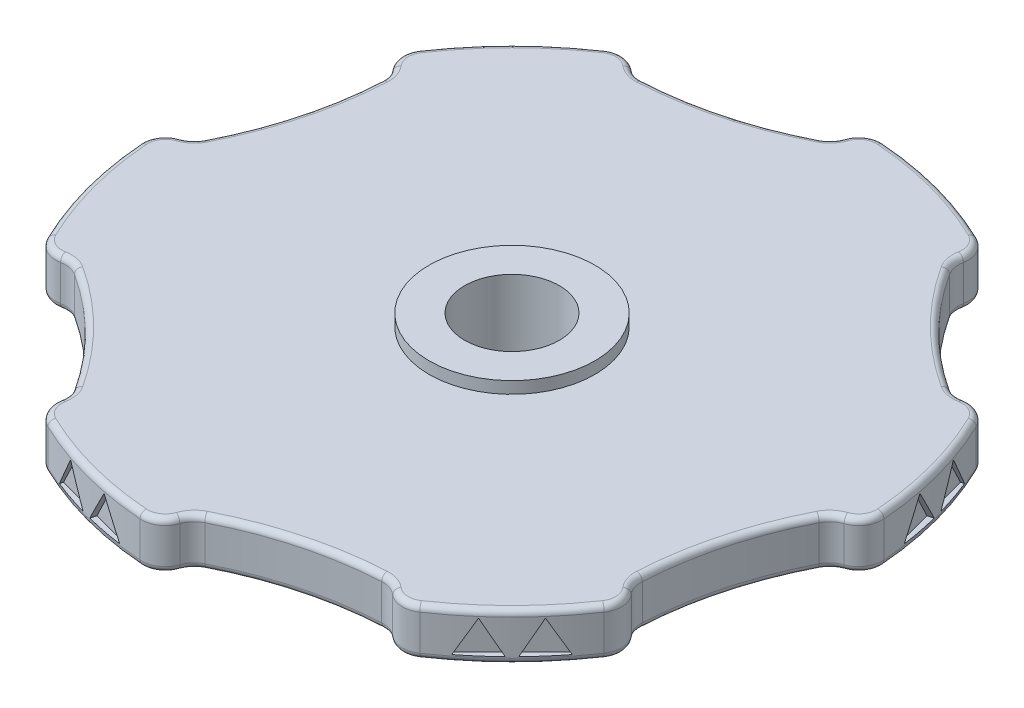
SolidWorks part; units mm, degrees
material "ABS"
ref_plane "前视基准面" through (0, 0, 0) normal (0, 0, 1) x (1, 0, 0)
ref_plane "上视基准面" through (0, 0, 0) normal (0, 1, 0) x (1, 0, 0)
ref_plane "右视基准面" through (0, 0, 0) normal (1, 0, 0) x (0, 0, -1)
other "Configuration Table"
sketch "草图1" plane through (0, 0, 0) normal (0, 1, 0) x (1, 0, 0)
  line L0 (0, 0) -> (0, -27.2667)
  line L1 (29.34, 0) -> (25.4092, 14.67) construction
  line L2 (25.4092, 14.67) -> (14.67, 25.4092) construction
  line L3 (14.67, 25.4092) -> (0, 29.34) construction
  line L4 (0, 29.34) -> (-14.67, 25.4092) construction
  line L5 (-14.67, 25.4092) -> (-25.4092, 14.67) construction
  line L6 (-25.4092, 14.67) -> (-29.34, 0) construction
  line L7 (-29.34, 0) -> (-25.4092, -14.67) construction
  line L8 (-25.4092, -14.67) -> (-14.67, -25.4092) construction
  line L9 (-14.67, -25.4092) -> (0, -29.34) construction
  line L10 (0, -29.34) -> (14.67, -25.4092) construction
  line L11 (14.67, -25.4092) -> (25.4092, -14.67) construction
  line L12 (25.4092, -14.67) -> (29.34, 0) construction
  line L13 (0, 0) -> (-13.6334, -23.6137)
  line L14 (13.6334, -23.6137) -> (0, 0)
  line L15 (0, 0) -> (-23.6137, -13.6334)
  line L16 (0, 0) -> (-27.2667, 0)
  line L17 (-13.6334, -23.6137) -> (0, 0)
  line L18 (0, 0) -> (-23.6137, 13.6334)
  line L19 (0, 0) -> (-13.6334, 23.6137)
  line L20 (-27.2667, 0) -> (0, 0)
  line L21 (0, 0) -> (0, 27.2667)
  line L22 (0, 0) -> (13.6334, 23.6137)
  line L23 (-13.6334, 23.6137) -> (0, 0)
  line L24 (0, 0) -> (23.6137, 13.6334)
  line L25 (0, 0) -> (27.2667, 0)
  line L26 (13.6334, 23.6137) -> (0, 0)
  line L27 (0, 0) -> (23.6137, -13.6334)
  line L28 (0, 0) -> (13.6334, -23.6137)
  line L29 (27.2667, 0) -> (0, 0)
  circle A1 centre (0, 0) radius 29.34 construction
  arc A2 (-12.7719, -26.4143) -> (-2.1463, -29.2614) centre (0, 0) ccw
  arc A3 (0, -27.2667) -> (-2.1463, -29.2614) centre (-2, -27.2667) cw
  arc A4 (-13.6334, -23.6137) -> (-12.7719, -26.4143) centre (-11.9013, -24.6137) ccw
  arc A5 (0, -29.34) -> (12.7719, -26.4143) centre (0, 0) ccw
  arc A6 (12.7719, -26.4143) -> (13.6334, -23.6137) centre (11.9013, -24.6137) ccw
  arc A7 (0, -27.2667) -> (13.6334, -23.6137) centre (14.1875, -52.9485) cw
  arc A8 (-29.2614, -2.1463) -> (-26.4143, -12.7719) centre (0, 0) ccw
  arc A9 (-27.2667, 0) -> (-29.2614, -2.1463) centre (-27.2667, -2) ccw
  arc A10 (-23.6137, -13.6334) -> (-26.4143, -12.7719) centre (-24.6137, -11.9013) cw
  arc A11 (-23.6137, -13.6334) -> (-13.6334, -23.6137) centre (-38.761, -38.761) cw
  arc A12 (-16.4895, 24.268) -> (-24.268, 16.4895) centre (0, 0) ccw
  arc A13 (-13.6334, 23.6137) -> (-16.4895, 24.268) centre (-15.3654, 22.6137) ccw
  arc A14 (-23.6137, 13.6334) -> (-24.268, 16.4895) centre (-22.6137, 15.3654) cw
  arc A15 (-23.6137, 13.6334) -> (-27.2667, 0) centre (-52.9485, 14.1875) cw
  arc A16 (12.7719, 26.4143) -> (2.1463, 29.2614) centre (0, 0) ccw
  arc A17 (13.6334, 23.6137) -> (12.7719, 26.4143) centre (11.9013, 24.6137) ccw
  arc A18 (0, 27.2667) -> (2.1463, 29.2614) centre (2, 27.2667) cw
  arc A19 (0, 27.2667) -> (-13.6334, 23.6137) centre (-14.1875, 52.9485) cw
  arc A20 (29.2614, 2.1463) -> (26.4143, 12.7719) centre (0, 0) ccw
  arc A21 (27.2667, 0) -> (29.2614, 2.1463) centre (27.2667, 2) ccw
  arc A22 (23.6137, 13.6334) -> (26.4143, 12.7719) centre (24.6137, 11.9013) cw
  arc A23 (23.6137, 13.6334) -> (13.6334, 23.6137) centre (38.761, 38.761) cw
  arc A24 (16.4895, -24.268) -> (24.268, -16.4895) centre (0, 0) ccw
  arc A25 (13.6334, -23.6137) -> (16.4895, -24.268) centre (15.3654, -22.6137) ccw
  arc A26 (23.6137, -13.6334) -> (24.268, -16.4895) centre (22.6137, -15.3654) cw
  arc A27 (23.6137, -13.6334) -> (27.2667, 0) centre (52.9485, -14.1875) cw
  point P70 (0, 0)
  dimension "D1" = 58.68
  dimension "D2" = 2
  dimension "D3" = 2
  dimension "D4" = 6
extrude "凸台-拉伸2" add sketch "草图1" along normal blind 4 contours A10 L15 L16 A9 A8 | L15 A11 L13 | L13 A4 A2 A3 L0 | L0 A7 L14 | A26 L27 L14 A25 A24 | L27 A27 L25 | A22 L24 L25 A21 A20 | L24 A23 L22 | A18 L21 L22 A17 A16 | L21 A19 L19 | A14 L18 L19 A13 A12 | L18 A15 L16
fillet "圆角2" radius 2 12 edges at (13.6334, 2, 23.6137) (0, 2, 27.2667) (-13.6334, 2, 23.6137) (-23.6137, 2, 13.6334) (-27.2667, 2, 0) (-23.6137, 2, -13.6334) (-13.6334, 2, -23.6137) (0, 2, -27.2667) (13.6334, 2, -23.6137) (23.6137, 2, -13.6334) (27.2667, 2, 0) (23.6137, 2, 13.6334)
fillet "圆角1" radius 0.5 72 edges at (24.6105, 4, 15.2518) (20.7465, 4, 20.7465) (15.2518, 4, 24.6105) (6.5937, 4, 24.6082) (-0.9032, 4, 28.9392) (-7.5938, 4, 28.3403) (-13.6874, 4, 25.5137) (-18.0145, 4, 18.0145) (-25.5137, 4, 13.6874) (-28.3403, 4, 7.5938) (-28.9392, 4, 0.9032) (-24.6082, 4, -6.5937) (-24.6105, 4, -15.2518) (-20.7465, 4, -20.7465) (-15.2518, 4, -24.6105) (-6.5937, 4, -24.6082) (0.9032, 4, -28.9392) (7.5938, 4, -28.3403) (13.6874, 4, -25.5137) (18.0145, 4, -18.0145) (25.5137, 4, -13.6874) (28.3403, 4, -7.5938) (28.9392, 4, -0.9032) (24.6082, 4, 6.5937) (28.9392, 0, -0.9032) (28.3403, 0, -7.5938) (25.5137, 0, -13.6874) (18.0145, 0, -18.0145) (13.6874, 0, -25.5137) (7.5938, 0, -28.3403) (0.9032, 0, -28.9392) (-6.5937, 0, -24.6082) (-15.2518, 0, -24.6105) (-20.7465, 0, -20.7465) (-24.6105, 0, -15.2518) (-24.6082, 0, -6.5937) (-28.9392, 0, 0.9032) (-28.3403, 0, 7.5938) (-25.5137, 0, 13.6874) (-18.0145, 0, 18.0145) (-13.6874, 0, 25.5137) (-7.5938, 0, 28.3403) (-0.9032, 0, 28.9392) (6.5937, 0, 24.6082) (15.2518, 0, 24.6105) (20.7465, 0, 20.7465) (24.6105, 0, 15.2518) (24.6082, 0, 6.5937) (13.403, 4, 23.7532) (0.2693, 4, 27.2724) (-13.8694, 4, 23.4839) (-23.4839, 4, 13.8694) (-27.2724, 4, -0.2693) (-23.7532, 4, -13.403) (-13.403, 4, -23.7532) (-0.2693, 4, -27.2724) (13.8694, 4, -23.4839) (23.4839, 4, -13.8694) (27.2724, 4, 0.2693) (23.7532, 4, 13.403) (27.2724, 0, 0.2693) (23.4839, 0, -13.8694) (13.8694, 0, -23.4839) (-0.2693, 0, -27.2724) (-13.403, 0, -23.7532) (-23.7532, 0, -13.403) (-27.2724, 0, -0.2693) (-23.4839, 0, 13.8694) (-13.8694, 0, 23.4839) (0.2693, 0, 27.2724) (13.403, 0, 23.7532) (23.7532, 0, 13.403)
sketch "草图2" plane through (0, 0, 0) normal (0, -1, 0) x (1, 0, 0)
  circle A0 centre (0, 0) radius 4
  dimension "D1" = 8
extrude "切除-拉伸1" cut sketch "草图2" against normal through all
sketch "草图4" plane through (0, 4, 0) normal (0, 1, 0) x (1, 0, 0)
  circle A1 centre (0, 0) radius 4 construction
  circle A2 centre (0, 0) radius 4
  circle A3 centre (0, 0) radius 7
  dimension "D1" = 3
extrude "凸台-拉伸3" add sketch "草图4" against normal offset from surface (6 mm away) 1 from offset 1
sketch "草图5" plane through (0, 0, 0) normal (0, 1, 0) x (1, 0, 0)
  line L0 (0, 0) -> (-10.0601, -37.545) construction
  line L1 (0, 0) -> (0, -39.386) construction
  dimension "D1" = 15
ref_plane "基准面1" through (-7.5938, 0, 28.3403) normal (-0.2588, 0, 0.9659) x (0.9659, 0, 0.2588)
sketch "草图7" plane through (-7.5938, 0, 28.3403) normal (-0.2588, 0, 0.9659) x (0.9659, 0, 0.2588)
  line L0 (-2, 3.3856) -> (-3.6, 0.6144)
  line L1 (-3.6, 0.6144) -> (-0.4, 0.6144)
  line L2 (-0.4, 0.6144) -> (-2, 3.3856)
  line L3 (-2, 0.6144) -> (-2, 0) construction
  line L4 (-2, 3.3856) -> (-2, 4) construction
  line L5 (-7.4412, 4) -> (-18.1871, 4) construction
  line L6 (3.6, 0.6144) -> (2, 3.3856)
  line L7 (2, 3.3856) -> (0.4, 0.6144)
  line L8 (0.4, 0.6144) -> (3.6, 0.6144)
  line L9 (-0.4, 0.6144) -> (3.6, 0.6144) construction
  line L10 (0, 1.9887) -> (0, 0) construction
  dimension "D1" = 3.2
  dimension "D3" = 4
  dimension "D2" = 2
extrude "切除-拉伸2" cut sketch "草图7" against normal blind 0.5
fillet "圆角3" [suppressed] radius 0.2
fillet "圆角4" [suppressed] radius 0.2
pattern_circular "阵列(圆周)3" count 6 every 60 about axis through (0, 0, 0) along (0, 1, 0) of "切除-拉伸2"
